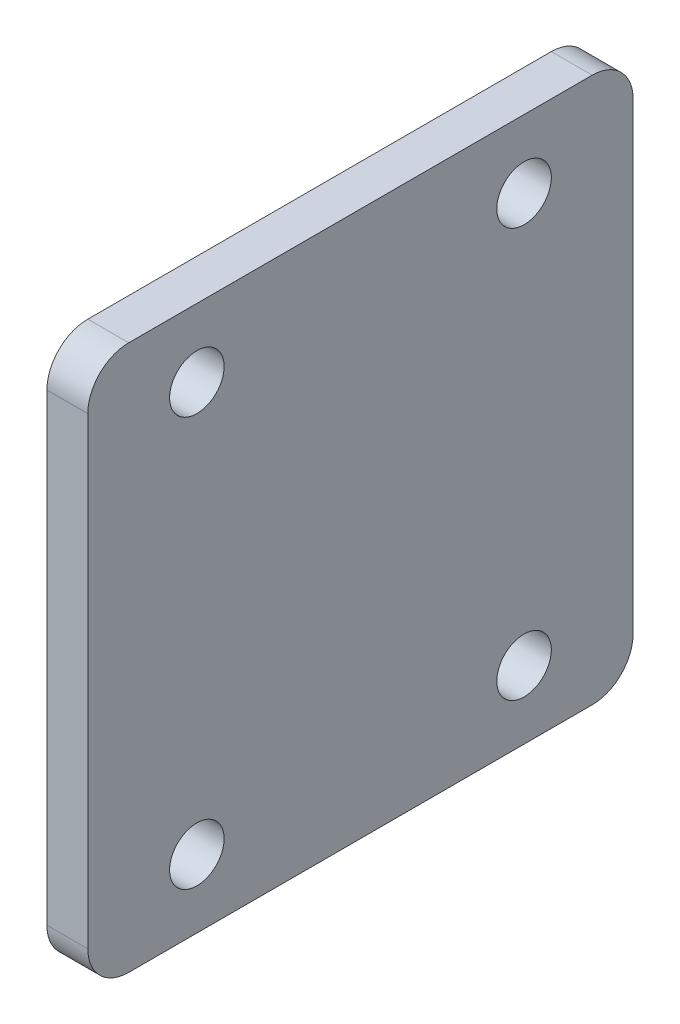
SolidWorks part; units mm, degrees
ref_plane "Front Plane" through (0, 0, 0) normal (0, 0, 1) x (1, 0, 0)
ref_plane "Top Plane" through (0, 0, 0) normal (0, 1, 0) x (1, 0, 0)
ref_plane "Right Plane" through (0, 0, 0) normal (1, 0, 0) x (0, 0, -1)
sketch "Sketch1" plane through (-26.0517, 0, 0) normal (-1, 0, 0) x (0, 0, 1)
  line L0 (-61.1631, 1220.2617) -> (-21.1631, 1220.2617) construction
  line L1 (-56.1631, 1220.2617) -> (-16.1631, 1220.2617)
  line L2 (-56.1631, 1220.2617) -> (-56.1631, 1180.2617)
  line L3 (-56.1631, 1180.2617) -> (-16.1631, 1180.2617)
  line L4 (-16.1631, 1220.2617) -> (-16.1631, 1180.2617)
  line L5 (-21.1631, 1180.2617) -> (-11.1631, 1180.2617) construction
  line L6 (-61.1631, 1220.2617) -> (-61.1631, 1180.2617) construction
  dimension "D1" = 40
  dimension "D2" = 5
extrude "Boss-Extrude1" add sketch "Sketch1" along normal blind 3
fillet "Fillet1" radius 3 4 edges at (-27.5517, 1180.2617, -16.1631) (-27.5517, 1180.2617, -56.1631) (-27.5517, 1220.2617, -56.1631) (-27.5517, 1220.2617, -16.1631)
sketch "Sketch2" plane through (-29.0517, 0, 0) normal (-1, 0, 0) x (0, 0, 1)
  circle A0 centre (-48.1631, 1215.2617) radius 2
  circle A1 centre (-24.1631, 1215.2617) radius 2
  circle A2 centre (-24.1631, 1185.2617) radius 2
  circle A3 centre (-48.1631, 1185.2617) radius 2
  dimension "D1" = 4
  dimension "D2" = 4
  dimension "D3" = 4
  dimension "D4" = 4
extrude "Cut-Extrude1" cut sketch "Sketch2" against normal up to next
